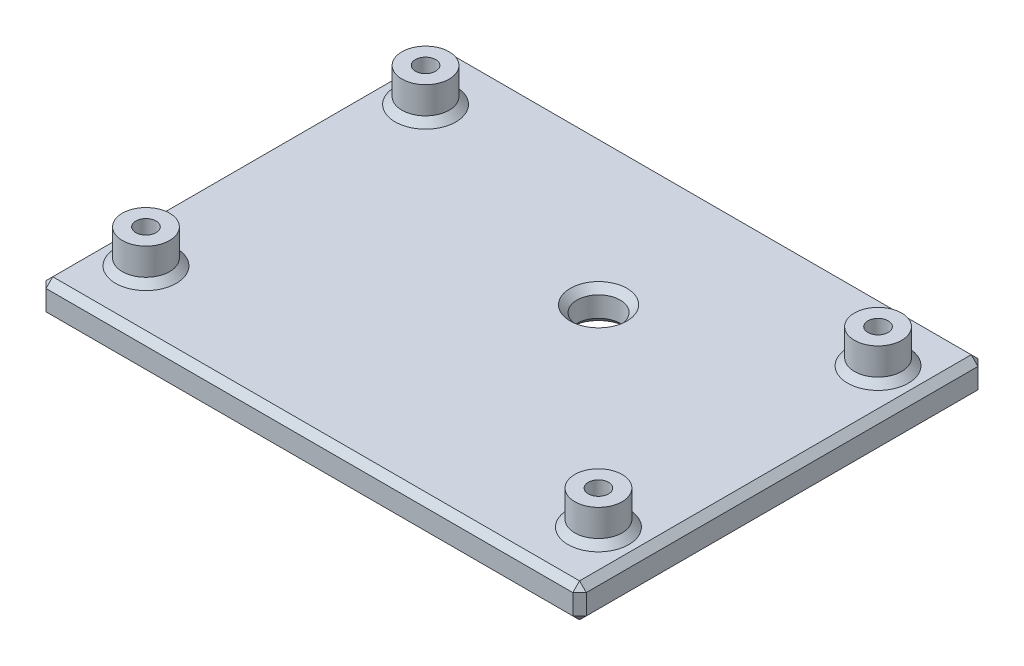
SolidWorks part; units mm, degrees
ref_plane "Front Plane" through (0, 0, 0) normal (0, 0, 1) x (1, 0, 0)
ref_plane "Top Plane" through (0, 0, 0) normal (0, 1, 0) x (1, 0, 0)
ref_plane "Right Plane" through (0, 0, 0) normal (1, 0, 0) x (0, 0, -1)
sketch "ProtoBoardSke" plane through (0, 0, 0) normal (0, 1, 0) x (1, 0, 0)
  line L0 (-33.5, 20.7) -> (33.5, 20.7) construction
  line L1 (-35.955, -23.445) -> (35.955, -23.445)
  line L2 (-35.955, -23.445) -> (-35.955, 23.445)
  line L3 (-35.955, 23.445) -> (35.955, 23.445)
  line L4 (35.955, -23.445) -> (35.955, 23.445)
  line L5 (-35.955, -23.445) -> (35.955, 23.445) construction
  line L6 (-35.955, 23.445) -> (35.955, -23.445) construction
  line L7 (33.5, 20.7) -> (33.5, -20.7) construction
  line L8 (33.5, -20.7) -> (-33.5, -20.7) construction
  line L9 (-33.5, -20.7) -> (-33.5, 20.7) construction
  line L10 (-33.5, 0) -> (0, 0) construction
  line L11 (0, 20.7) -> (0, 0) construction
  circle A0 centre (-33.5, 20.7) radius 1.5
  circle A1 centre (33.5, 20.7) radius 1.5
  circle A2 centre (33.5, -20.7) radius 1.5
  circle A3 centre (-33.5, -20.7) radius 1.5
  point P0 (0, 0)
  point P8 (-33.5, 22.2)
  point P15 (-33.5, -22.2)
  point P16 (35, 20.7)
  point P18 (-35, 20.7)
  point P22 (0, 0)
  point P23 (-0.4488, -0.2927)
  dimension "D4" = 3
  dimension "D5" = 70
  dimension "D1" = 71.91
  dimension "D2" = 46.89
  dimension "D3" = 44.4
sketch "EncoderPositionSke" plane through (0, 0, 0) normal (0, 1, 0) x (1, 0, 0)
  line L0 (-35.955, 23.445) -> (35.955, 23.445) construction
  line L1 (-1.005, 1.825) -> (10.995, 1.825)
  line L2 (-1.005, 1.825) -> (-1.005, 13.825)
  line L3 (-1.005, 13.825) -> (10.995, 13.825)
  line L4 (10.995, 1.825) -> (10.995, 13.825)
  line L5 (-1.005, 1.825) -> (10.995, 13.825) construction
  line L6 (-1.005, 13.825) -> (10.995, 1.825) construction
  line L7 (35.955, -23.445) -> (35.955, 23.445) construction
  circle A0 centre (4.995, 7.825) radius 3
  point P0 (4.995, 7.825)
  dimension "D5" = 6
  dimension "D1" = 21.62
  dimension "D2" = 36.96
  dimension "D4" = 12
sketch "Sketch3" plane through (0, 0, 0) normal (0, 1, 0) x (1, 0, 0)
  line L1 (-40, -30) -> (40, -30)
  line L2 (-40, -30) -> (-40, 30)
  line L3 (-40, 30) -> (40, 30)
  line L4 (40, -30) -> (40, 30)
  line L5 (-40, -30) -> (40, 30) construction
  line L6 (-40, 30) -> (40, -30) construction
  point P0 (0, 0)
  dimension "D1" = 60
  dimension "D2" = 80
extrude "Boss-Extrude1" add sketch "Sketch3" along normal blind 5
sketch "Sketch5" plane through (0, 5, 0) normal (0, 1, 0) x (1, 0, 0)
  circle A0 centre (-33.5, -20.7) radius 1.5 construction
  circle A1 centre (33.5, -20.7) radius 1.5 construction
  circle A2 centre (33.5, 20.7) radius 1.5 construction
  circle A3 centre (-33.5, 20.7) radius 1.5 construction
  circle A4 centre (33.5, 20.7) radius 3.5
  circle A5 centre (33.5, -20.7) radius 3.5
  circle A6 centre (-33.5, -20.7) radius 3.5
  circle A7 centre (-33.5, 20.7) radius 3.5
  circle A24 centre (33.5, 20.7) radius 1.5 construction
  circle A25 centre (33.5, -20.7) radius 1.5 construction
  circle A26 centre (-33.5, -20.7) radius 1.5 construction
  circle A27 centre (-33.5, 20.7) radius 1.5 construction
  dimension "D1" = 2
extrude "Boss-Extrude2" add sketch "Sketch5" along normal blind 5
sketch "Sketch6" plane through (0, 0, 0) normal (0, 1, 0) x (1, 0, 0)
  circle A0 centre (33.5, -20.7) radius 1.5 construction
  circle A1 centre (33.5, 20.7) radius 1.5 construction
  circle A2 centre (4.995, 7.825) radius 3 construction
  circle A3 centre (-33.5, -20.7) radius 1.5 construction
  circle A4 centre (-33.5, 20.7) radius 1.5 construction
  circle A5 centre (33.5, -20.7) radius 1.5
  circle A6 centre (33.5, 20.7) radius 1.5
  circle A7 centre (4.995, 7.825) radius 3 construction
  circle A8 centre (-33.5, -20.7) radius 1.5
  circle A9 centre (-33.5, 20.7) radius 1.5
  circle A10 centre (4.995, 7.825) radius 3.2
  dimension "D1" = 0.2
extrude "Cut-Extrude1" cut sketch "Sketch6" along normal through all
chamfer "Chamfer1" distance 1 angle 45 22 edges at (0, 5, 30) (-40, 5, 0) (0, 5, -30) (40, 5, 0) (33.5, 5, -24.2) (33.5, 5, 17.2) (-33.5, 5, 17.2) (-33.5, 5, -24.2) (4.995, 5, -11.025) (0, 0, -30) (-40, 0, 0) (0, 0, 30) (40, 0, 0) (33.5, 0, 22.2) (4.995, 0, -4.625) (-33.5, 0, -19.2) (-33.5, 0, 22.2) (33.5, 0, -19.2) (-40, 2.5, -30) (-40, 2.5, 30) (40, 2.5, -30) (40, 2.5, 30)
